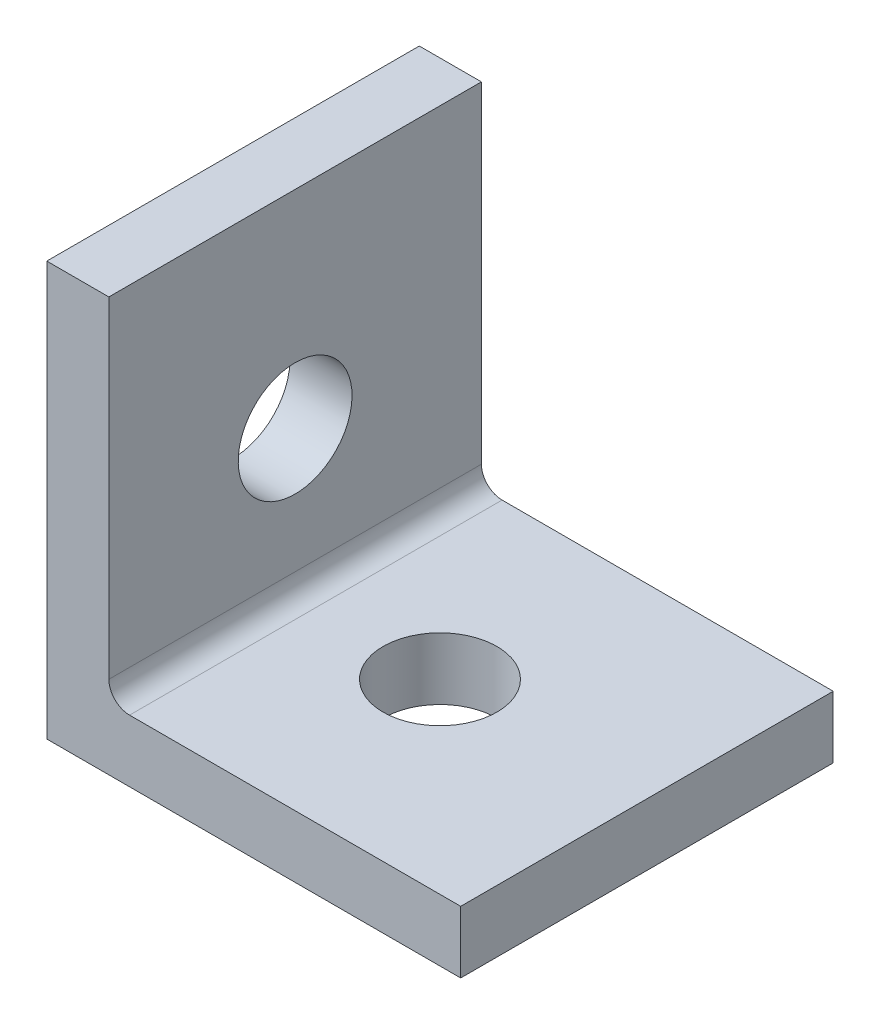
SolidWorks part; units mm, degrees
material "6063-T5"
ref_plane "Front Plane" through (0, 0, 0) normal (0, 0, 1) x (1, 0, 0)
ref_plane "Top Plane" through (0, 0, 0) normal (0, 1, 0) x (1, 0, 0)
ref_plane "Right Plane" through (0, 0, 0) normal (1, 0, 0) x (0, 0, -1)
sketch "Sketch1" plane through (0, 0, 0) normal (0, 0, 1) x (1, 0, 0)
  line L0 (0, 0) -> (0, 20)
  line L1 (0, 20) -> (3, 20)
  line L2 (3, 20) -> (3, 4)
  line L3 (4, 3) -> (20, 3)
  line L4 (20, 3) -> (20, 0)
  line L5 (20, 0) -> (0, 0)
  arc A0 (4, 3) -> (3, 4) centre (4, 4) cw
  dimension "D5" = 1
  dimension "D1" = 20
  dimension "D2" = 20
  dimension "D3" = 3
  dimension "D4" = 3
extrude "Boss-Extrude1" add sketch "Sketch1" along normal mid plane 18
sketch "Sketch2" plane through (0, 3, 0) normal (0, 1, 0) x (1, 0, 0)
  line L0 (0, -9) -> (0, 9) construction
  line L1 (20, 9) -> (4, 9) construction
  circle A0 centre (10, 0) radius 2.75
  dimension "D1" = 10
  dimension "D3" = 5.5
  dimension "D2" = 9
extrude "Cut-Extrude1" cut sketch "Sketch2" against normal through all
sketch "Sketch3" plane through (3, 0, 0) normal (1, 0, 0) x (0, 0, -1)
  line L0 (-9, 0) -> (9, 0) construction
  line L1 (9, 4) -> (9, 20) construction
  circle A0 centre (0, 10) radius 2.75
  dimension "D1" = 10
  dimension "D3" = 5.5
  dimension "D2" = 9
extrude "Cut-Extrude2" cut sketch "Sketch3" against normal through all
